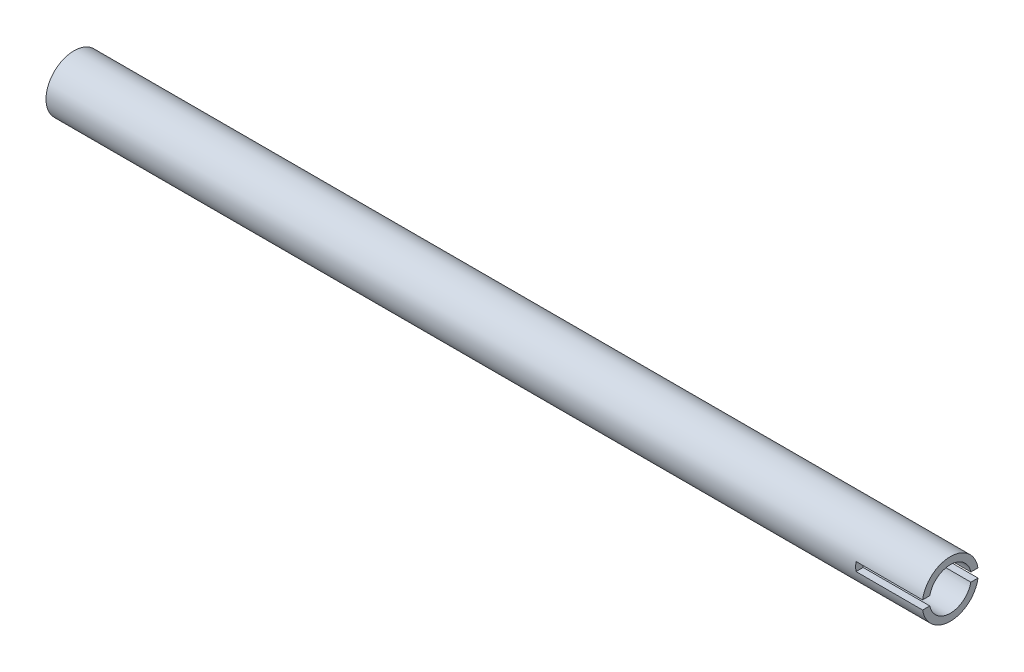
SolidWorks part; units mm, degrees
material "1.0037 (S235JR)"
ref_plane "Front Plane" through (0, 0, 0) normal (0, 0, 1) x (1, 0, 0)
ref_plane "Top Plane" through (0, 0, 0) normal (0, 1, 0) x (1, 0, 0)
ref_plane "Right Plane" through (0, 0, 0) normal (1, 0, 0) x (0, 0, -1)
sketch "Sketch1" plane through (0, 0, 0) normal (1, 0, 0) x (0, 0, -1)
  circle A0 centre (0, 0) radius 8
  circle A1 centre (0, 0) radius 6
  dimension "D1" = 16
  dimension "D2" = 2
extrude "Boss-Extrude1" add sketch "Sketch1" along normal mid plane 250
sketch "Sketch2" plane through (0, 0, 0) normal (0, 0, 1) x (1, 0, 0)
  line L1 (125, 1.25) -> (106, 1.25)
  line L2 (125, 1.25) -> (125, -1.25)
  line L3 (125, -1.25) -> (106, -1.25)
  line L4 (106, 1.25) -> (106, -1.25)
  line L5 (125, -8) -> (125, 8) construction
  line L6 (125, 0) -> (0, 0) construction
  dimension "D1" = 2.5
  dimension "D2" = 19
extrude "Cut-Extrude1" cut sketch "Sketch2" against normal through all both and the other way through all
ref_plane "Plane1" through (0, 0, -8) normal (0, 0, -1) x (-1, 0, 0)
